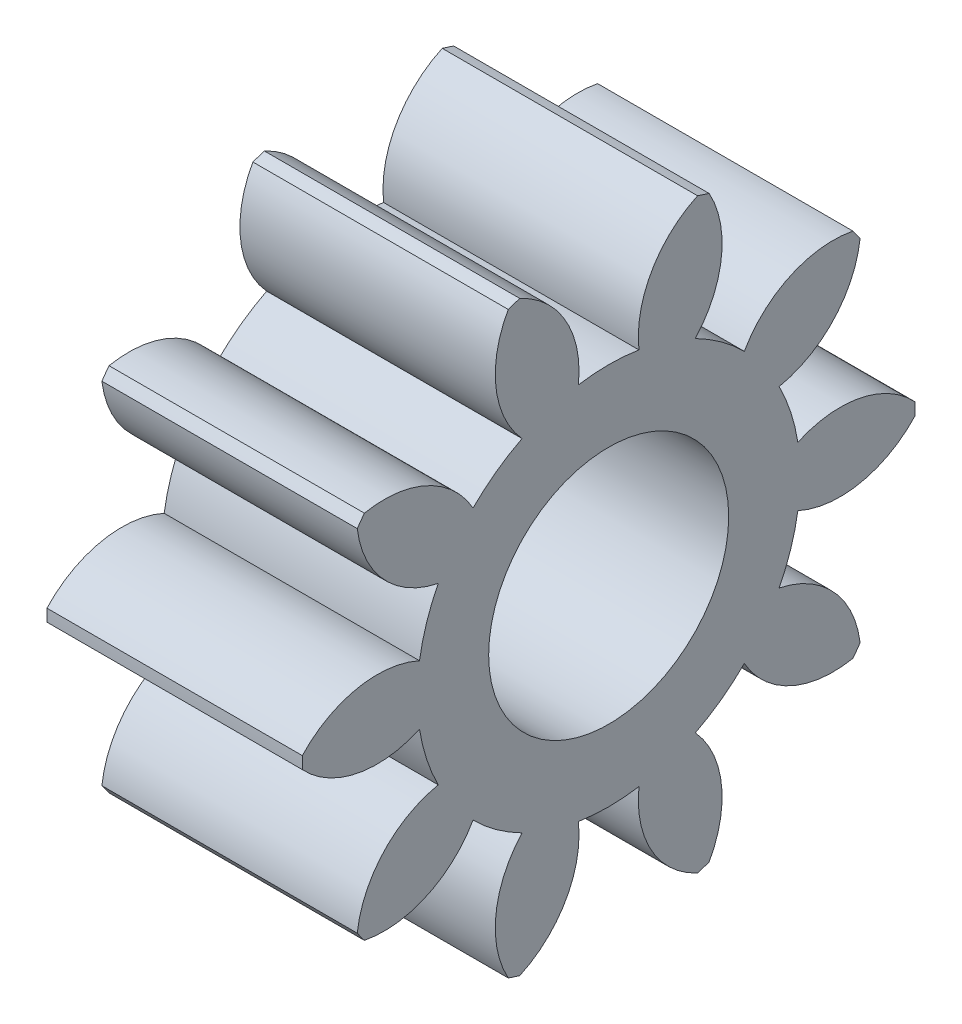
SolidWorks part; units mm, degrees
ref_plane "Plane1" through (0, 0, 0) normal (0, 0, 1) x (1, 0, 0)
ref_plane "Plane2" through (0, 0, 0) normal (0, 1, 0) x (1, 0, 0)
ref_plane "Plane3" through (0, 0, 0) normal (1, 0, 0) x (0, 0, -1)
other "Configuration Table"
sketch "HoldingSke" plane through (0, 0, 0) normal (0, 1, 0) x (1, 0, 0)
  line L0 (0, 0) -> (0.9848, -0.1736)
  line L1 (-15, 0) -> (100, 0) construction
  line L2 (0, 0) -> (-2.1039, 2.3779)
  line L3 (0, 0) -> (-11.863, 4.5341)
  line L4 (0, 0) -> (8.5048, 1.4996)
  line L5 (0, 0) -> (-46.8476, -17.4728)
  line L6 (0, 0) -> (-4.1448, -2.7965)
  line L7 (-2.1039, 2.3779) -> (8.6586, 51.2059)
  line L8 (-76.2, 54.61) -> (-76.1, 54.61)
  line L9 (-71.009, 38.7566) -> (-53.1078, 45.2721)
  line L10 (-76.2, 71.12) -> (104.1128, 71.12)
  line L11 (0, 0) -> (-5, 0)
  line L12 (-76.2, 101.6) -> (-76.162, 101.6)
  line L13 (24.9733, 27.94) -> (52.9518, 28.4284)
  line L14 (24.9733, 27.94) -> (24.9743, 27.94)
  line L15 (24.9733, 27.94) -> (100.4006, 29.5858)
  line L16 (-63.627, -1) -> (-12.827, -1)
  circle A0 centre (0, 0) radius 0.4
  circle A1 centre (0, 0) radius 3.749
  circle A2 centre (0, 0) radius 37.5
  circle A3 centre (0, 0) radius 0.4
  dimension "MHD" = 7.498
  dimension "Hub_dia" = 75
  dimension "Bore" = 0.8
  dimension "MBD" = 0.8
  dimension "Num_teeth" = 10
  dimension "Pitch" = 1
  dimension "Overall_len" = 50
  dimension "Show_teeth" = 10
  dimension "Thickness" = 5
  dimension "OAL" = 50.0001
  dimension "T_dim" = 0.1
  dimension "Ap" = 20
  dimension "H" = 19.05
  dimension "Pitch_radius" = 180.3128
  dimension "Width" = 5
  dimension "Backlash" = 0.038
  dimension "Addendum_fac" = 1
  dimension "Dedendum_fac" = 1.25
  dimension "Clearance_fac" = 0.25
  dimension "Dedendum_add" = 0.001
  dimension "Module" = 1
sketch "BasProSke" plane through (0, 0, 0) normal (0, 1, 0) x (1, 0, 0)
  line L0 (-10, 0) -> (60, 0) construction
  line L1 (0, 0) -> (0, 6)
  line L2 (0, 0) -> (5, 0)
  line L3 (5, 0) -> (5, 6)
  line L4 (5, 6) -> (0, 6)
  dimension "Thickness" = 5
  dimension "Diameter" = 12
revolve "Base-Revolve" add sketch "BasProSke" angle 360 about L0
sketch "TooCutSke" plane through (0, 0, 0) normal (1, 0, 0) x (0, 0, -1)
  line L1 (0, 0) -> (0, 107) construction
  line L2 (0, 0) -> (-0.8485, 4.9275) construction
  line L3 (0, 0) -> (-3.0584, 9.4126) construction
  line L4 (-0.8485, 4.9275) -> (-1.5292, 4.7063) construction
  arc A0 (0.5928, 3.7018) -> (-0.5928, 3.7018) centre (0, 0) ccw
  arc A1 (1.7758, 5.7578) -> (-1.7758, 5.7578) centre (0, 0) ccw
  circle A2 centre (0, 0) radius 5 construction
  circle A3 centre (0, 0) radius 4.6985 construction
  arc A4 (-0.5928, 3.7018) -> (-1.7758, 5.7578) centre (-2.5801, 3.9267) ccw
  arc A5 (1.7758, 5.7578) -> (0.5928, 3.7018) centre (2.5801, 3.9267) ccw
  dimension "Root_dia" = 7.498
  dimension "Overcut_dia" = 12.0508
  dimension "Pitch_dia" = 10
  dimension "Base_dia" = 9.3969
  dimension "Flank_rad" = 2
  dimension "Half_ang" = 18
  dimension "Half_CT" = 0.7157
extrude "ToothCut" cut sketch "TooCutSke" along normal through all
fillet "Breaks" [suppressed] radius 0.02
fillet "RootFillets" [suppressed] radius 0.251
pattern_circular "TeethCuts" count 10 every 36 about axis through (-10, 0, 0) along (1, 0, 0) of "ToothCut", "RootFillets", "Breaks"
sketch "HubNeaOneSke" plane through (0, 0, 0) normal (-1, 0, 0) x (0, 0, 1)
  circle A0 centre (0, 0) radius 3.749
  dimension "Diameter" = 7.498
extrude "HubNearOne" [suppressed] add sketch "HubNeaOneSke" along normal blind 45.0001
sketch "HubNeaBotSke" plane through (0, 0, 0) normal (-1, 0, 0) x (0, 0, 1)
  circle A0 centre (0, 0) radius 3.749
  dimension "Diameter" = 7.498
extrude "HubNearBoth" [suppressed] add sketch "HubNeaBotSke" along normal blind 22.5
ref_plane "FarPln" through (5, 0, 0) normal (1, 0, 0) x (0, 0, -1)
sketch "HubFarSke" plane through (5, 0, 0) normal (1, 0, 0) x (0, 0, -1)
  circle A0 centre (0, 0) radius 3.749
  dimension "Diameter" = 7.498
extrude "HubFar" [suppressed] add sketch "HubFarSke" along normal blind 22.5
sketch "BorSke" plane through (0, 0, 0) normal (1, 0, 0) x (0, 0, -1)
  circle A0 centre (0, 0) radius 0.4
  dimension "Diameter" = 0.8
extrude "Bore" cut sketch "BorSke" along normal mid plane 100.0001
sketch "KeySke" plane through (0, 0, 0) normal (1, 0, 0) x (0, 0, -1)
  line L0 (-0.05, 0) -> (-0.05, 0.5)
  line L1 (-0.05, 0.5) -> (0.05, 0.5)
  line L2 (0.05, 0.5) -> (0.05, 0)
  line L3 (0, 0) -> (0, 34) construction
  line L4 (-0.05, 0) -> (0.05, 0)
  dimension "Offset" = 0.5
  dimension "Width" = 0.1
extrude "Keyway" [suppressed] cut sketch "KeySke" along normal mid plane 100.0001
pattern_circular "Keyway2" [suppressed] count 2 every 90 about axis through (-10, 0, 0) along (1, 0, 0)
sketch "Sketch1" plane through (5, 0, 0) normal (1, 0, 0) x (0, 0, -1)
  circle A0 centre (0, 0) radius 2.35
  dimension "D1" = 4.7
extrude "Cut-Extrude1" cut sketch "Sketch1" against normal through all
equation "' \"Module@HoldingSke\" = 6.35"
equation "' \"Num_teeth@HoldingSke\" = 12"
equation "' \"Ap@HoldingSke\" =  20"
equation "' \"Ap@HoldingSke\" = 20"
equation "' \"Width@HoldingSke\" = 0.5 * 25.4"
equation "' \"Hub_dia@HoldingSke\"= 1 * 25.4"
equation "' \"Hub_dia@HoldingSke\" = 1 * 25.4"
equation "' \"Overall_len@HoldingSke\" = 1.0 * 25.4"
equation "' \"Bore@HoldingSke\" = 0.75 * 25.4"
equation "' \"T_dim@HoldingSke\" = 0.1 * 25.4"
equation "' \"Width@KeySke\" = 0.25 * 25.4"
equation "' \"Show_teeth@HoldingSke\" = 13"
equation "' \"Backlash@HoldingSke\" = 0.009 * 25.4"
equation "' \"Addendum_fac@HoldingSke\" = 1.0"
equation "' \"Dedendum_fac@HoldingSke\" = 1.25"
equation "' \"Dedendum_add@HoldingSke\" = 0.00005 * 25.4"
equation "' \"Clearance_fac@HoldingSke\" = 0.25"
equation "\"Pitch@HoldingSke\" = 1 / \"Module@HoldingSke\""
equation "\"Overcut_dia@TooCutSke\" = (\"Num_teeth@HoldingSke\" + 2 * \"Addendum_fac@HoldingSke\") / \"Pitch@HoldingSke\" + 0.002 * 25.4"
equation "\"Pitch_dia@TooCutSke\" = \"Num_teeth@HoldingSke\" / \"Pitch@HoldingSke\""
equation "\"Base_dia@TooCutSke\" = \"Num_teeth@HoldingSke\" / \"Pitch@HoldingSke\" * cos((\"Ap@HoldingSke\"  * 3.14159265 / 180))"
equation "\"Root_dia@TooCutSke\" = (\"Num_teeth@HoldingSke\" + 2) / \"Pitch@HoldingSke\" - 2 * (\"Addendum_fac@HoldingSke\" + \"Dedendum_fac@HoldingSke\") / \"Pitch@HoldingSke\" - \"Dedendum_add@HoldingSke\" * 2"
equation "\"Half_ang@TooCutSke\" = 180 / \"Num_teeth@HoldingSke\""
equation "\"Half_CT@TooCutSke\" = \"Num_teeth@HoldingSke\" / \"Pitch@HoldingSke\" * sin((3.14159265 / 2 / \"Num_teeth@HoldingSke\")) / 2 - 7 * \"Backlash@HoldingSke\" / 4"
equation "\"Flank_rad@TooCutSke\" = \"Num_teeth@HoldingSke\" / \"Pitch@HoldingSke\" / 5"
equation "\"Radius@RootFillets\" = \"Clearance_fac@HoldingSke\" / \"Pitch@HoldingSke\" + \"Dedendum_add@HoldingSke\""
equation "\"Break_rad@Breaks\" = 0.02 / \"Pitch@HoldingSke\""
equation "\"Thickness@HoldingSke\" = \"Width@HoldingSke\""
equation "\"OAL@HoldingSke\" = \"Thickness@HoldingSke\""
equation "\"MHD@HoldingSke\" = (\"Num_teeth@HoldingSke\" + 2) / \"Pitch@HoldingSke\" - 2 * (\"Addendum_fac@HoldingSke\" + \"Dedendum_fac@HoldingSke\")  / \"Pitch@HoldingSke\" - \"Dedendum_add@HoldingSke\" * 2"
equation "\"MBD@HoldingSke\" = (\"Num_teeth@HoldingSke\" + 2) / \"Pitch@HoldingSke\" - 2 * (\"Addendum_fac@HoldingSke\" + \"Dedendum_fac@HoldingSke\")  / \"Pitch@HoldingSke\" - \"Dedendum_add@HoldingSke\" * 2 - 0.002 * 25.4"
equation "\"MHD@HoldingSke\" = ((sgn( \"MHD@HoldingSke\" - \"Hub_dia@HoldingSke\" )-1)*( \"MHD@HoldingSke\" - \"Hub_dia@HoldingSke\" ))/-2+ \"Hub_dia@HoldingSke\""
equation "\"MBD@HoldingSke\" = ((sgn( \"MBD@HoldingSke\" - \"Bore@HoldingSke\" )-1)*( \"MBD@HoldingSke\" - \"Bore@HoldingSke\" ))/-2+ \"Bore@HoldingSke\""
equation "\"OAL@HoldingSke\" = ((sgn( \"OAL@HoldingSke\" - \"Overall_len@HoldingSke\" )+1)*( \"OAL@HoldingSke\" - \"Overall_len@HoldingSke\" ))/2 + \"Overall_len@HoldingSke\" + 0.000002 * 25.4"
equation "\"Num_teeth@TeethCuts\" = int( \"Show_teeth@HoldingSke\" ) + 1"
equation "\"Num_teeth@TeethCuts\" = ((sgn( \"Num_teeth@TeethCuts\" - \"Num_teeth@HoldingSke\" )-1)*( \"Num_teeth@TeethCuts\" - \"Num_teeth@HoldingSke\" ))/-2+ \"Num_teeth@HoldingSke\""
equation "\"Num_teeth@TeethCuts\" = ((sgn( \"Num_teeth@TeethCuts\" - 2.0)+1)*( \"Num_teeth@TeethCuts\" - 2.0))/2 +2.0"
equation "\"Angle@TeethCuts\" = 360.0 / \"Num_teeth@HoldingSke\""
equation "\"Diameter@BasProSke\" = (\"Num_teeth@HoldingSke\" + 2 * \"Addendum_fac@HoldingSke\") / \"Pitch@HoldingSke\""
equation "\"Thickness@BasProSke\"  = \"Thickness@HoldingSke\""
equation "' \"Fillet_rad@BasProSke\" =  \"Thickness@HoldingSke\" * 0.05"
equation "' \"Fillet_rad@BasProSke\" = \"Thickness@HoldingSke\" * 0.05"
equation "\"MHD@HoldingSke\" = ((sgn( \"MHD@HoldingSke\" - \"Root_dia@TooCutSke\" )-1)*( \"MHD@HoldingSke\" - \"Root_dia@TooCutSke\" ))/-2+ \"Root_dia@TooCutSke\""
equation "\"Diameter@HubNeaOneSke\" = \"MHD@HoldingSke\""
equation "\"Length@HubNearOne\" = \"OAL@HoldingSke\" - \"Thickness@BasProSke\""
equation "\"Diameter@HubNeaBotSke\" = \"MHD@HoldingSke\""
equation "\"Length@HubNearBoth\" = ( \"OAL@HoldingSke\" - \"Thickness@BasProSke\" ) / 2.0"
equation "\"Thickness@FarPln\" = \"Thickness@BasProSke\""
equation "\"Diameter@HubFarSke\" = \"MHD@HoldingSke\""
equation "\"Length@HubFar\" = ( \"OAL@HoldingSke\" - \"Thickness@BasProSke\" ) / 2.0"
equation "\"Diameter@BorSke\" = \"MBD@HoldingSke\""
equation "\"D1@Bore\" = \"OAL@HoldingSke\" * 2.0"
equation "\"D1@Keyway\" = \"OAL@HoldingSke\" * 2.0"
equation "\"Offset@KeySke\" = \"T_dim@HoldingSke\" + \"MBD@HoldingSke\" / 2.0"
